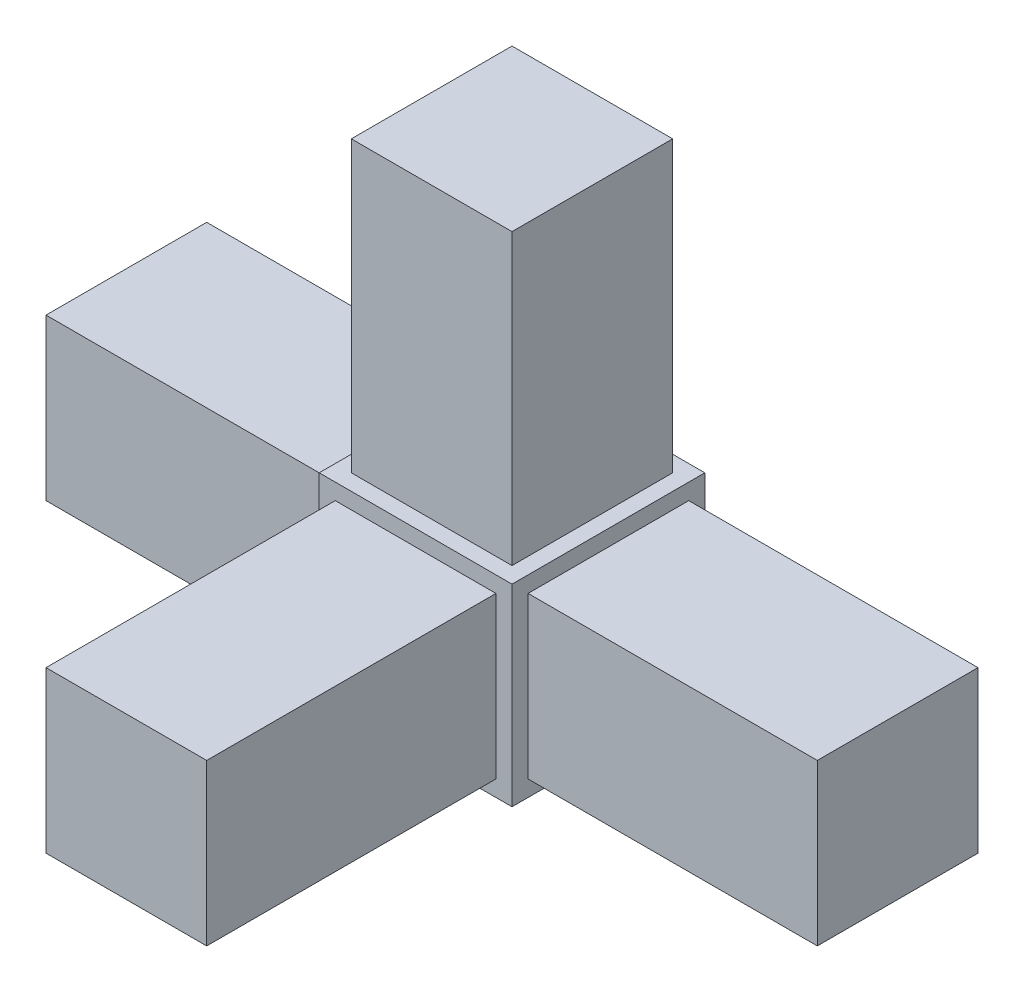
SolidWorks part; units mm, degrees
material "ABS"
ref_plane "Front Plane" through (0, 0, 0) normal (0, 0, 1) x (1, 0, 0)
ref_plane "Top Plane" through (0, 0, 0) normal (0, 1, 0) x (1, 0, 0)
ref_plane "Right Plane" through (0, 0, 0) normal (1, 0, 0) x (0, 0, -1)
sketch "Sketch1" plane through (0, 0, 0) normal (0, 0, 1) x (1, 0, 0)
  line L1 (9.525, -9.525) -> (-9.525, -9.525)
  line L2 (9.525, -9.525) -> (9.525, 9.525)
  line L3 (9.525, 9.525) -> (-9.525, 9.525)
  line L4 (-9.525, -9.525) -> (-9.525, 9.525)
  line L5 (9.525, -9.525) -> (-9.525, 9.525) construction
  line L6 (9.525, 9.525) -> (-9.525, -9.525) construction
  point P0 (0, 0)
  dimension "D1" = 19.05
extrude "Boss-Extrude1" add sketch "Sketch1" along normal blind 19.05
sketch "Sketch2" plane through (0, 9.525, 0) normal (0, 1, 0) x (1, 0, 0)
  line L0 (-9.525, 0) -> (9.525, -19.05) construction
  line L2 (-7.9375, -1.5875) -> (7.9375, -1.5875)
  line L3 (-7.9375, -1.5875) -> (-7.9375, -17.4625)
  line L4 (-7.9375, -17.4625) -> (7.9375, -17.4625)
  line L5 (7.9375, -1.5875) -> (7.9375, -17.4625)
  line L6 (-7.9375, -1.5875) -> (7.9375, -17.4625) construction
  line L7 (-7.9375, -17.4625) -> (7.9375, -1.5875) construction
  point P4 (0, -9.525)
  dimension "D1" = 15.875
extrude "Boss-Extrude2" add sketch "Sketch2" along normal blind 28.575
sketch "Sketch3" plane through (9.525, 0, 0) normal (1, 0, 0) x (0, 0, -1)
  line L0 (-19.05, 9.525) -> (0, -9.525) construction
  line L2 (-17.4625, -7.9375) -> (-1.5875, -7.9375)
  line L3 (-17.4625, -7.9375) -> (-17.4625, 7.9375)
  line L4 (-17.4625, 7.9375) -> (-1.5875, 7.9375)
  line L5 (-1.5875, -7.9375) -> (-1.5875, 7.9375)
  line L6 (-17.4625, -7.9375) -> (-1.5875, 7.9375) construction
  line L7 (-17.4625, 7.9375) -> (-1.5875, -7.9375) construction
  point P4 (-9.525, 0)
  dimension "D1" = 15.875
extrude "Boss-Extrude3" add sketch "Sketch3" along normal blind 28.575
sketch "Sketch4" plane through (0, 0, 19.05) normal (0, 0, 1) x (1, 0, 0)
  line L0 (-9.525, 9.525) -> (9.525, -9.525) construction
  line L2 (7.9375, -7.9375) -> (-7.9375, -7.9375)
  line L3 (7.9375, -7.9375) -> (7.9375, 7.9375)
  line L4 (7.9375, 7.9375) -> (-7.9375, 7.9375)
  line L5 (-7.9375, -7.9375) -> (-7.9375, 7.9375)
  line L6 (7.9375, -7.9375) -> (-7.9375, 7.9375) construction
  line L7 (7.9375, 7.9375) -> (-7.9375, -7.9375) construction
  point P4 (0, 0)
  dimension "D1" = 15.875
extrude "Boss-Extrude4" add sketch "Sketch4" along normal blind 28.575
sketch "Sketch5" plane through (-9.525, 0, 0) normal (-1, 0, 0) x (0, 0, 1)
  line L0 (1.5875, 7.9375) -> (17.4625, 7.9375) construction
  line L1 (1.5875, 7.9375) -> (17.4625, 7.9375)
  line L2 (1.5875, 7.9375) -> (1.5875, -7.9375)
  line L3 (1.5875, -7.9375) -> (17.4625, -7.9375)
  line L4 (17.4625, 7.9375) -> (17.4625, -7.9375)
  line L5 (1.5875, -7.9375) -> (1.5875, 7.9375) construction
  line L6 (9.525, -9.525) -> (9.525, -7.9375) construction
  line L7 (19.05, -9.525) -> (0, -9.525) construction
  line L8 (1.5875, 0) -> (0, 0) construction
extrude "Boss-Extrude5" add sketch "Sketch5" along normal blind 28.575
equation "\"Height\"= 32in"
equation "\"Width\"= 23in"
equation "\"Depth\"= 20in"
equation "\"Plexi\"= .121in"
equation "\"MagnetThickness\"= .125in"
equation "\"MagnetDiameter\"= 12mm"
equation "\"DoorPlexi\" = \"Plexi\""
equation "\"BasePlateThickness\" = 0.5in"
equation "\"BasePlateWidth\" = \"Width\"+\"EBWidth\"-2*\"Plexi\""
equation "\"BasePlateDepth\" = \"TopBarDepth\"+2*\"CornerCube\""
equation "\"Boxsize\" = .75in"
equation "\"Boxinner\" = .625in"
equation "\"CornerCube\" = 0.75in"
equation "\"FingerLength\" = 1.125in"
equation "\"Cutwidth\"= .016in"
equation "\"Earsize\"= 1in + \"Cutwidth\" /2"
equation "\"Slotsize\" = 1in - \"CutWidth\" / 2"
equation "\"InnerWidth\" = \"Width\" - 2* \"Plexi\""
equation "\"InnerHeight\" = \"Height\" -2 * \"Plexi\""
equation "\"InnerDepth\" = \"Depth\" - 2*\"Plexi\""
equation "\"RearNumHoles\" = 4"
equation "\"RearHolesBorder\" = 2.25"
equation "\"RearHoleSpacing\" = (\"Width\" - 2*\"RearHolesBorder\") / (\"RearNumHoles\"-1)"
equation "\"RearBarLength\" = (\"InnerWidth\"-2*\"CornerCube\")"
equation "\"RearTopNumHoles\" = 4"
equation "\"RearTopHolesBorder\" = 3.1"
equation "\"RearTopHolesSpacing\" = (\"Width\" - 2*\"RearTopHolesBorder\") / (\"RearTopNumHoles\"-1)"
equation "\"SideTopNumHoles\" = 4"
equation "\"SideTopHoleOffset\"=\"CornerCube\"+\"FingerLength\"+\"Plexi\"+.5"
equation "\"SideTopHoleSpacing\" = (\"TopBarDepth\"-2*\"SideTopHoleOffset\") / (\"SideTopNumHoles\"-1)"
equation "\"SideHorizNumHoles\" = 4"
equation "\"SideHorizHoleBorder\" = 1.50"
equation "\"SideHorizHoleSpacing\" = (\"TopBarDepth\"-2*\"SideHorizHoleBorder\") / (\"SideHorizNumHoles\"-1)"
equation "\"SideVertBarLength\"=\"Height\"-\"BasePlateThickness\"-2*\"CornerCube\"-\"Plexi\""
equation "\"SideVertNumHoles\" = 4"
equation "\"SideVertHolesBorder\" = \"CornerCube\"+\"FingerLength\"+1.50"
equation "\"SideVertHoleSpacing\" = (\"InnerHeight\" - 2*\"SideVertHolesBorder\") / (\"SideVertNumHoles\"-1)"
equation "\"RearSideVertNumHoles\" = 4"
equation "\"RearSideVertHolesBorder\" = 2.4"
equation "\"RearSideVertHoleSpacing\" = (\"InnerHeight\" - 2*\"RearSideVertHolesBorder\") / (\"RearSideVertNumHoles\"-1)"
equation "\"RivetDia\" = .228in"
equation "\"SlotDepth\" = \"Plexi\" + 0.75in + .005in"
equation "\"SideSlotWidth\"   = \"Plexi\"+.005in"
equation "\"SidePanelVertSpacing\" = (\"Height\"-2*(1.75-\"Plexi\")) / 5"
equation "\"BottomPanelSideHoleSpacing\" = (\"InnerDepth\"-2*(1.75-\"Plexi\")) / 4"
equation "\"FrontDoorGap\" = .1in"
equation "\"TopDepth\" = \"Depth\"-\"DoorPlexi\"-\"FrontDoorGap\""
equation "\"TopBarDepth\" = \"Depth\"-\"DoorPlexi\"-\"Plexi\"-2*\"MagnetThickness\"-2*\"CornerCube\""
equation "\"D1@Boss-Extrude1\"=\"CornerCube\""
equation "\"D1@Sketch1\"=\"CornerCube\""
equation "\"D1@Boss-Extrude4\"=\"FingerLength\""
equation "\"D1@Boss-Extrude3\"=\"FingerLength\""
equation "\"D1@Boss-Extrude2\"=\"FingerLength\""
equation "\"D1@Boss-Extrude5\"=\"FingerLength\""
equation "\"D1@Sketch2\"=\"Boxinner\""
equation "\"D1@Sketch4\"=\"Boxinner\""
equation "\"D1@Sketch3\"=\"Boxinner\""
